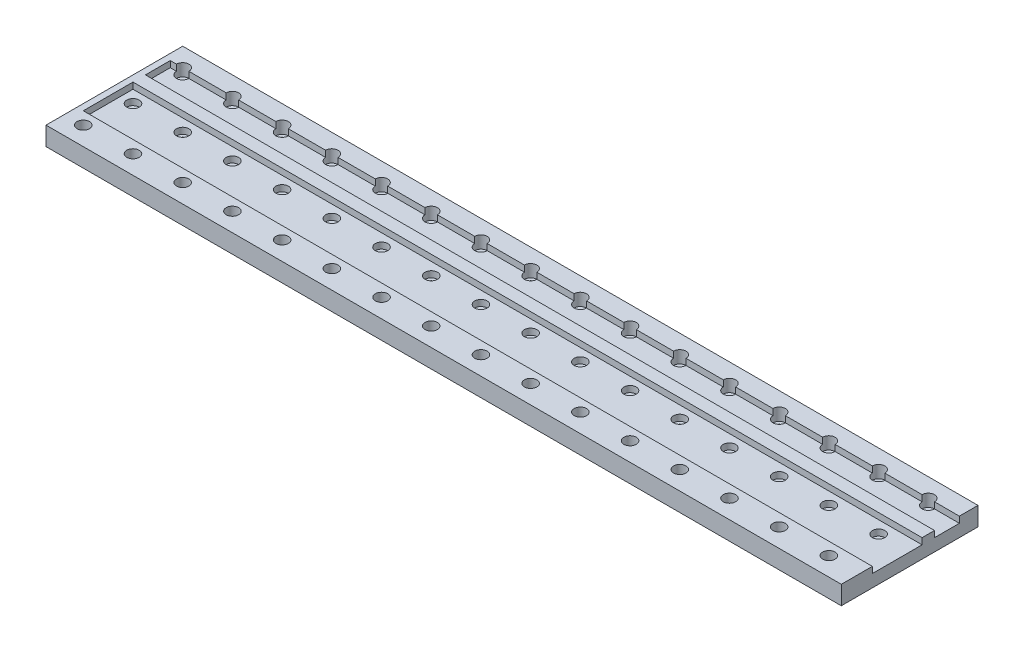
SolidWorks part; units mm, degrees
ref_plane "Front Plane" through (0, 0, 0) normal (0, 0, 1) x (1, 0, 0)
ref_plane "Top Plane" through (0, 0, 0) normal (0, 1, 0) x (1, 0, 0)
ref_plane "Right Plane" through (0, 0, 0) normal (1, 0, 0) x (0, 0, -1)
sketch "Sketch1" plane through (0, 0, 0) normal (0, 1, 0) x (1, 0, 0)
  line L1 (0, 0) -> (812.8, 0)
  line L2 (0, 0) -> (0, 139.7)
  line L3 (0, 139.7) -> (812.8, 139.7)
  line L4 (812.8, 0) -> (812.8, 139.7)
  dimension "D1" = 139.7
  dimension "D2" = 812.8
extrude "Boss-Extrude1" add sketch "Sketch1" along normal blind 19.05
sketch "Sketch2" plane through (0, 19.05, 0) normal (0, 1, 0) x (1, 0, 0)
  line L0 (0, 139.7) -> (0, 0) construction
  line L5 (0, 19.05) -> (812.8, 19.05) construction
  line L10 (812.8, 0) -> (812.8, 139.7) construction
  line L11 (0, 0) -> (812.8, 0) construction
  line L12 (0, 69.85) -> (812.8, 69.85) construction
  line L13 (812.8, 120.65) -> (0, 120.65) construction
  line L14 (0, 120.65) -> (812.8, 120.65) construction
  line L15 (6.35, 31.75) -> (812.8, 31.75)
  line L16 (6.35, 31.75) -> (6.35, 82.55)
  line L17 (6.35, 82.55) -> (812.8, 82.55)
  line L18 (812.8, 31.75) -> (812.8, 82.55)
  line L19 (6.35, 95.25) -> (812.8, 95.25)
  line L20 (6.35, 95.25) -> (6.35, 120.65)
  line L21 (6.35, 120.65) -> (812.8, 120.65)
  line L22 (812.8, 95.25) -> (812.8, 120.65)
  dimension "D9" = 50.8
  dimension "D1" = 19.05
  dimension "D2" = 50.8
  dimension "D3" = 50.8
  dimension "D4" = 50.8
  dimension "D5" = 25.4
  dimension "D6" = 6.35
  dimension "D7" = 12.7
  dimension "D8" = 12.7
extrude "Cut-Extrude1" cut sketch "Sketch2" against normal blind 6.35
sketch "Sketch3" plane through (0, 19.05, 0) normal (0, 1, 0) x (1, 0, 0)
  line L0 (0, 19.05) -> (812.8, 19.05) construction
  line L1 (0, 69.85) -> (812.8, 69.85) construction
  line L2 (812.8, 120.65) -> (0, 120.65) construction
  line L3 (0, 139.7) -> (0, 0) construction
  circle A0 centre (19.05, 19.05) radius 6.35
  circle A1 centre (19.05, 69.85) radius 6.35
  circle A2 centre (19.05, 120.65) radius 6.35
  circle A3 centre (69.85, 19.05) radius 6.35
  circle A4 centre (69.85, 69.85) radius 6.35
  circle A5 centre (69.85, 120.65) radius 6.35
  circle A6 centre (120.65, 19.05) radius 6.35
  circle A7 centre (120.65, 69.85) radius 6.35
  circle A8 centre (120.65, 120.65) radius 6.35
  circle A9 centre (171.45, 19.05) radius 6.35
  circle A10 centre (171.45, 69.85) radius 6.35
  circle A11 centre (171.45, 120.65) radius 6.35
  circle A12 centre (222.25, 19.05) radius 6.35
  circle A13 centre (222.25, 69.85) radius 6.35
  circle A14 centre (222.25, 120.65) radius 6.35
  circle A15 centre (273.05, 19.05) radius 6.35
  circle A16 centre (273.05, 69.85) radius 6.35
  circle A17 centre (273.05, 120.65) radius 6.35
  circle A18 centre (323.85, 19.05) radius 6.35
  circle A19 centre (323.85, 69.85) radius 6.35
  circle A20 centre (323.85, 120.65) radius 6.35
  circle A21 centre (374.65, 19.05) radius 6.35
  circle A22 centre (374.65, 69.85) radius 6.35
  circle A23 centre (374.65, 120.65) radius 6.35
  circle A24 centre (425.45, 19.05) radius 6.35
  circle A25 centre (425.45, 69.85) radius 6.35
  circle A26 centre (425.45, 120.65) radius 6.35
  circle A27 centre (476.25, 19.05) radius 6.35
  circle A28 centre (476.25, 69.85) radius 6.35
  circle A29 centre (476.25, 120.65) radius 6.35
  circle A30 centre (527.05, 19.05) radius 6.35
  circle A31 centre (527.05, 69.85) radius 6.35
  circle A32 centre (527.05, 120.65) radius 6.35
  circle A33 centre (577.85, 19.05) radius 6.35
  circle A34 centre (577.85, 69.85) radius 6.35
  circle A35 centre (577.85, 120.65) radius 6.35
  circle A36 centre (628.65, 19.05) radius 6.35
  circle A37 centre (628.65, 69.85) radius 6.35
  circle A38 centre (628.65, 120.65) radius 6.35
  circle A39 centre (679.45, 19.05) radius 6.35
  circle A40 centre (679.45, 69.85) radius 6.35
  circle A41 centre (679.45, 120.65) radius 6.35
  circle A42 centre (730.25, 19.05) radius 6.35
  circle A43 centre (730.25, 69.85) radius 6.35
  circle A44 centre (730.25, 120.65) radius 6.35
  circle A45 centre (781.05, 19.05) radius 6.35
  circle A46 centre (781.05, 69.85) radius 6.35
  circle A47 centre (781.05, 120.65) radius 6.35
  dimension "D2" = 12.7
  dimension "D1" = 19.05
  dimension "D3" = 50.8
extrude "Cut-Extrude4" cut sketch "Sketch3" against normal blind 12.7
sketch "Sketch4" plane through (0, 6.35, 0) normal (0, 1, 0) x (1, 0, 0)
  circle A0 centre (19.05, 19.05) radius 2.8067
  circle A1 centre (19.05, 69.85) radius 2.8067
  circle A2 centre (19.05, 120.65) radius 2.8067
  circle A3 centre (69.85, 19.05) radius 2.8067
  circle A4 centre (69.85, 69.85) radius 2.8067
  circle A5 centre (69.85, 120.65) radius 2.8067
  circle A6 centre (120.65, 19.05) radius 2.8067
  circle A7 centre (120.65, 69.85) radius 2.8067
  circle A8 centre (120.65, 120.65) radius 2.8067
  circle A9 centre (171.45, 19.05) radius 2.8067
  circle A10 centre (171.45, 69.85) radius 2.8067
  circle A11 centre (171.45, 120.65) radius 2.8067
  circle A12 centre (222.25, 19.05) radius 2.8067
  circle A13 centre (222.25, 69.85) radius 2.8067
  circle A14 centre (222.25, 120.65) radius 2.8067
  circle A15 centre (273.05, 19.05) radius 2.8067
  circle A16 centre (273.05, 69.85) radius 2.8067
  circle A17 centre (273.05, 120.65) radius 2.8067
  circle A18 centre (323.85, 19.05) radius 2.8067
  circle A19 centre (323.85, 69.85) radius 2.8067
  circle A20 centre (323.85, 120.65) radius 2.8067
  circle A21 centre (374.65, 19.05) radius 2.8067
  circle A22 centre (374.65, 69.85) radius 2.8067
  circle A23 centre (374.65, 120.65) radius 2.8067
  circle A24 centre (425.45, 19.05) radius 2.8067
  circle A25 centre (425.45, 69.85) radius 2.8067
  circle A26 centre (425.45, 120.65) radius 2.8067
  circle A27 centre (476.25, 19.05) radius 2.8067
  circle A28 centre (476.25, 69.85) radius 2.8067
  circle A29 centre (476.25, 120.65) radius 2.8067
  circle A30 centre (527.05, 19.05) radius 2.8067
  circle A31 centre (527.05, 69.85) radius 2.8067
  circle A32 centre (527.05, 120.65) radius 2.8067
  circle A33 centre (577.85, 19.05) radius 2.8067
  circle A34 centre (577.85, 69.85) radius 2.8067
  circle A35 centre (577.85, 120.65) radius 2.8067
  circle A36 centre (628.65, 19.05) radius 2.8067
  circle A37 centre (628.65, 69.85) radius 2.8067
  circle A38 centre (628.65, 120.65) radius 2.8067
  circle A39 centre (679.45, 19.05) radius 2.8067
  circle A40 centre (679.45, 69.85) radius 2.8067
  circle A41 centre (679.45, 120.65) radius 2.8067
  circle A42 centre (730.25, 19.05) radius 2.8067
  circle A43 centre (730.25, 69.85) radius 2.8067
  circle A44 centre (730.25, 120.65) radius 2.8067
  circle A45 centre (781.05, 19.05) radius 2.8067
  circle A46 centre (781.05, 69.85) radius 2.8067
  circle A47 centre (781.05, 120.65) radius 2.8067
  dimension "D1" = 5.6134
  dimension "D2" = 50.8
extrude "Cut-Extrude5" cut sketch "Sketch4" against normal up to surface (6.35 mm away) up to face at (406.4, 0, -69.85)
